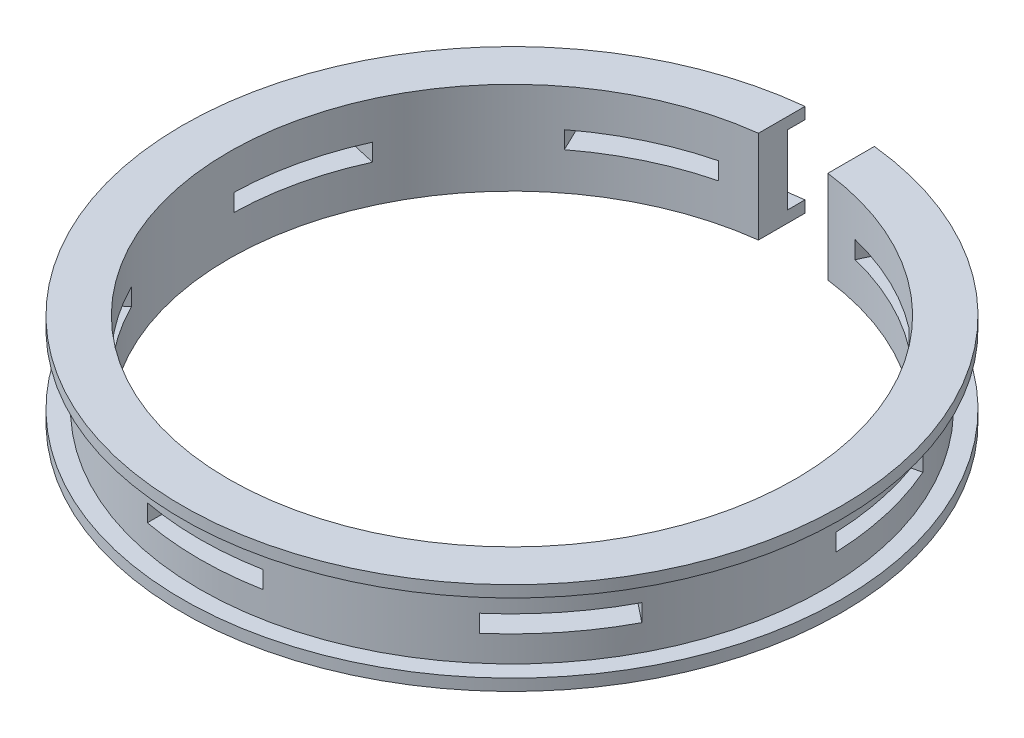
SolidWorks part; units mm, degrees
material "Сталь"
ref_plane "Спереди" through (0, 0, 0) normal (0, 0, 1) x (1, 0, 0)
ref_plane "Сверху" through (0, 0, 0) normal (0, 1, 0) x (1, 0, 0)
ref_plane "Справа" through (0, 0, 0) normal (1, 0, 0) x (0, 0, -1)
sketch "Эскиз1" plane through (0, 0, 0) normal (0, 0, 1) x (1, 0, 0)
  line L0 (0, 0) -> (0, 18.4038) construction
  line L1 (24.5, 0) -> (24.5, 8)
  line L2 (24.5, 8) -> (28.5, 8)
  line L3 (28.5, 8) -> (28.5, 7)
  line L4 (28.5, 7) -> (27, 7)
  line L5 (27, 7) -> (27, 1)
  line L6 (27, 1) -> (28.5, 1)
  line L7 (28.5, 1) -> (28.5, 0)
  line L8 (28.5, 0) -> (24.5, 0)
  dimension "D1" = 57
  dimension "D2" = 49
  dimension "D3" = 8
  dimension "D4" = 6
  dimension "D5" = 1.5
revolve "Повернуть1" add sketch "Эскиз1" angle 360 about L0
sketch "Эскиз2" plane through (0, 0, 0) normal (0, 1, 0) x (1, 0, 0)
  line L1 (3, 57) -> (-3, 57)
  line L2 (3, 57) -> (3, 0)
  line L3 (3, 0) -> (-3, 0)
  line L4 (-3, 57) -> (-3, 0)
  line L5 (3, 57) -> (-3, 0) construction
  line L6 (3, 0) -> (-3, 57) construction
  circle A0 centre (0, 0) radius 28.5 construction
  point P0 (0, 28.5)
  point P7 (0, 0)
  dimension "D1" = 6
extrude "Вырез-Вытянуть1" cut sketch "Эскиз2" along normal through all
sketch "Эскиз3" plane through (0, 0, 0) normal (0, 0, 1) x (1, 0, 0)
  line L0 (0, 8) -> (0, 0) construction
  line L1 (28.5, 8) -> (-28.5, 8) construction
  line L3 (-5, 3.25) -> (5, 3.25)
  line L4 (-5, 3.25) -> (-5, 4.75)
  line L5 (-5, 4.75) -> (5, 4.75)
  line L6 (5, 3.25) -> (5, 4.75)
  line L7 (-5, 3.25) -> (5, 4.75) construction
  line L8 (-5, 4.75) -> (5, 3.25) construction
  point P5 (0, 4)
  dimension "D1" = 10
  dimension "D2" = 1.5
extrude "Вырез-Вытянуть2" cut sketch "Эскиз3" along normal through all
pattern_circular "Круговой массив1" count 7 over 360 about axis through (0, 0, 0) along (0, 1, 0) of "Вырез-Вытянуть2"
